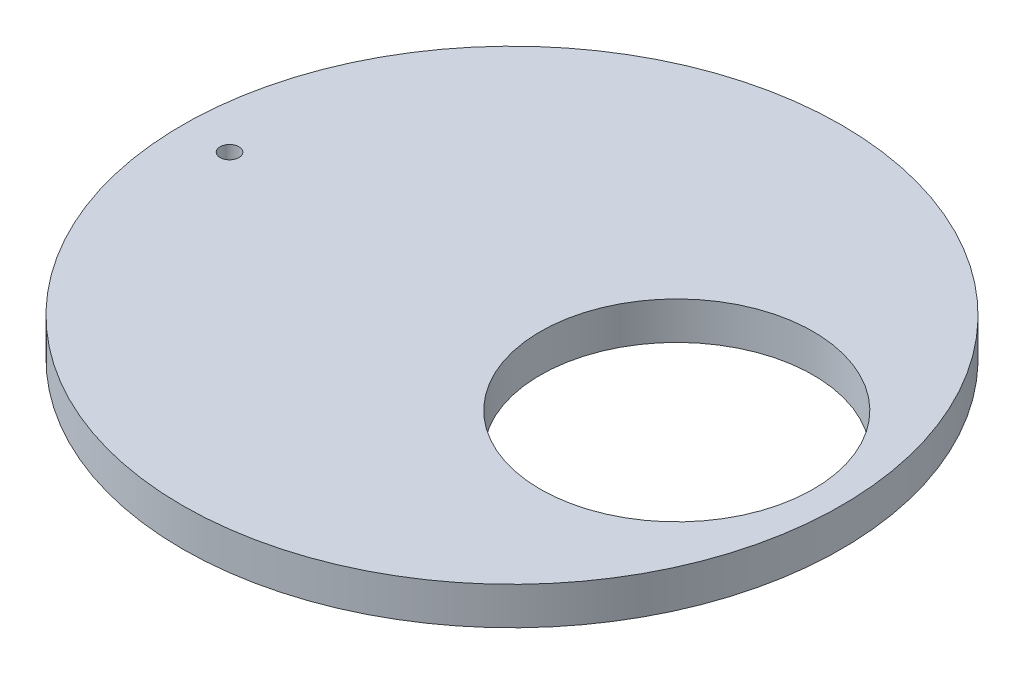
SolidWorks part; units mm, degrees
ref_plane "Front Plane" through (0, 0, 0) normal (0, 0, 1) x (1, 0, 0)
ref_plane "Top Plane" through (0, 0, 0) normal (0, 1, 0) x (1, 0, 0)
ref_plane "Right Plane" through (0, 0, 0) normal (1, 0, 0) x (0, 0, -1)
sketch "Sketch1" plane through (0, 0, 0) normal (0, 1, 0) x (1, 0, 0)
  circle A0 centre (0, 0) radius 70
  arc A1 (35, 29) -> (35, -29) centre (35, 0) ccw
  circle A2 centre (35, 0) radius 29
  dimension "D1" = 140
  dimension "D2" = 58
  dimension "D3" = 35
extrude "Boss-Extrude1" add sketch "Sketch1" along normal blind 8 contours A0 A2 A1
sketch "Sketch2" plane through (0, 8, 0) normal (0, 1, 0) x (1, 0, 0)
  circle A0 centre (-60, -0.0015) radius 2
  dimension "D1" = 4
extrude "Cut-Extrude1" cut sketch "Sketch2" against normal up to next
sketch "Sketch3" plane through (0, 0, 0) normal (0, -1, 0) x (1, 0, 0)
  circle A0 centre (-60, 0.0015) radius 2.4
  dimension "D1" = 4.8
extrude "Cut-Extrude2" cut sketch "Sketch3" against normal blind 2
